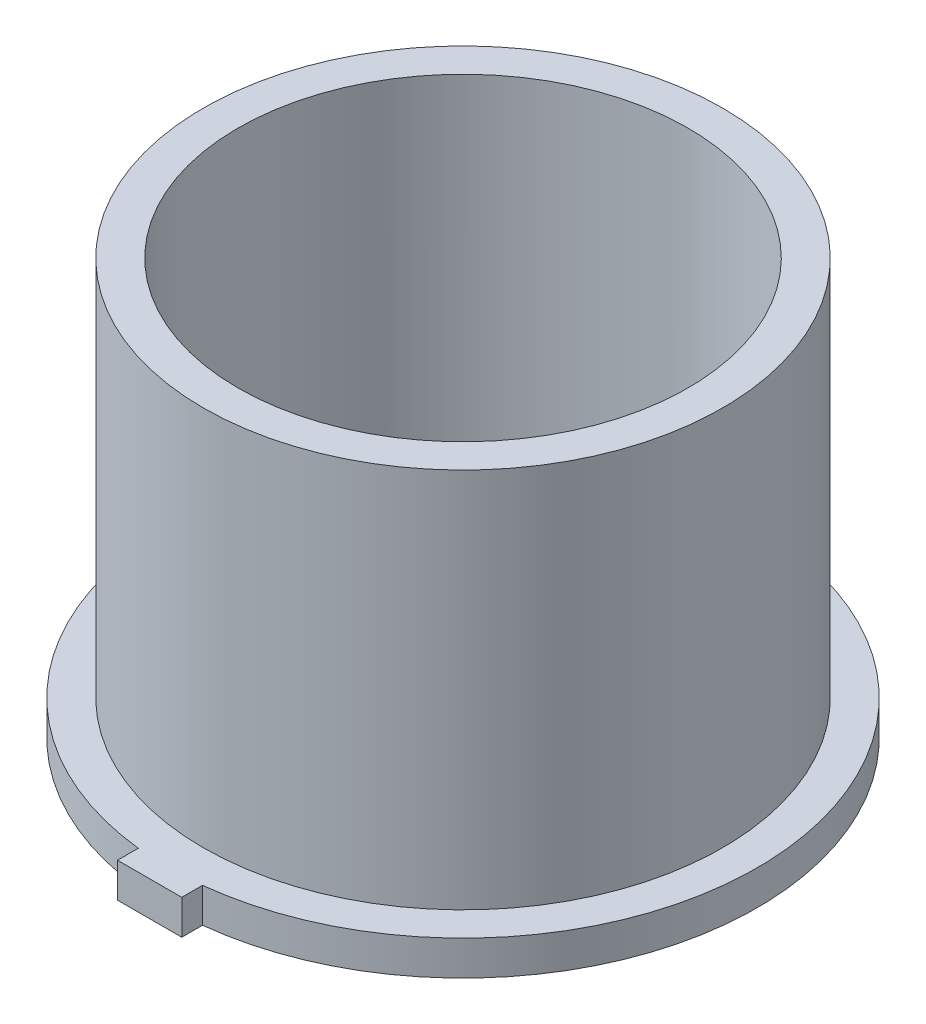
SolidWorks part; units mm, degrees
other "Markup1"
sketch "Sketch5" plane through (-30, 25, 30) normal (-0.0255, 0.5913, 0.806) x (0.9947, 0.0957, -0.0387)
ref_plane "Front Plane" through (0, 0, 0) normal (0, 0, 1) x (1, 0, 0)
ref_plane "Top Plane" through (0, 0, 0) normal (0, 1, 0) x (1, 0, 0)
ref_plane "Right Plane" through (0, 0, 0) normal (1, 0, 0) x (0, 0, -1)
sketch "Sketch1" plane through (0, 0, 0) normal (0, 1, 0) x (1, 0, 0)
  circle A0 centre (0, 0) radius 37.5
  circle A1 centre (0, 0) radius 32.5
  dimension "D1" = 65
  dimension "D2" = 75
sketch "Sketch4" plane through (0, 0, 0) normal (0, 1, 0) x (1, 0, 0)
  line L0 (0, 32.5) -> (0, -32.5) construction
  line L1 (-4.6363, 32.1676) -> (-4.6363, 9)
  line L2 (4.6363, 32.1676) -> (4.6363, 9)
  line L3 (4.6363, -9) -> (4.6363, -32.1676)
  line L4 (-10.3923, 0) -> (-5.1962, -9)
  line L5 (-5.1962, -9) -> (-4.6363, -9)
  line L6 (5.1962, -9) -> (10.3923, 0)
  line L7 (10.3923, 0) -> (5.1962, 9)
  line L8 (5.1962, 9) -> (4.6363, 9)
  line L9 (-5.1962, 9) -> (-10.3923, 0)
  line L10 (-4.6363, -9) -> (-4.6363, -32.1676)
  line L11 (4.6363, -9) -> (5.1962, -9)
  line L12 (-4.6363, 9) -> (-5.1962, 9)
  line L13 (-4.6363, -42.2464) -> (-4.6363, -45.2464)
  line L14 (-4.6363, -45.2464) -> (4.6363, -45.2464)
  line L15 (4.6363, -45.2464) -> (4.6363, -42.2464)
  line L16 (-10.3923, 0) -> (10.3923, 0) construction
  line L17 (-4.6363, 42.2464) -> (-4.6363, 45.2464)
  line L18 (-4.6363, 45.2464) -> (4.6363, 45.2464)
  line L19 (4.6363, 45.2464) -> (4.6363, 42.2464)
  arc A0 (4.6363, -42.2464) -> (4.6363, 42.2464) centre (0, 0) ccw
  arc A1 (4.6363, -32.1676) -> (4.6363, 32.1676) centre (0, 0) ccw
  arc A2 (-4.6363, 32.1676) -> (-4.6363, -32.1676) centre (0, 0) ccw
  circle A3 centre (0, 0) radius 9 construction
  arc A4 (-4.6363, 42.2464) -> (-4.6363, -42.2464) centre (0, 0) ccw
  dimension "D1" = 65
  dimension "D2" = 85
  dimension "D3" = 18
  dimension "D4" = 3
extrude "Boss-Extrude3" add sketch "Sketch4" along normal blind 5
ref_plane "Plane3" through (0, 0, 0) normal (0, -1, 0) x (-1, 0, 0)
sketch "Sketch7" plane through (0, 0, 0) normal (0, -1, 0) x (-1, 0, 0)
  line L1 (-7.5056, 0) -> (-3.7528, -6.5)
  line L2 (-3.7528, -6.5) -> (3.7528, -6.5)
  line L3 (3.7528, -6.5) -> (7.5056, 0)
  line L4 (7.5056, 0) -> (3.7528, 6.5)
  line L5 (3.7528, 6.5) -> (-3.7528, 6.5)
  line L6 (-3.7528, 6.5) -> (-7.5056, 0)
  circle A0 centre (0, 0) radius 6.5 construction
  dimension "D1" = 13
extrude "Cut-Extrude1" cut sketch "Sketch7" against normal through all
extrude "Boss-Extrude4" add sketch "Sketch1" along normal blind 60
equation "\"BallBearingDiameter\" = 22mm"
equation "\"SmallTubeOD\" = 75mm"
equation "\"SmallTubeID\"= \"SmallTubeOD\" - \"WallThickness\" * 2"
equation "\"D1@Sketch1\"=\"SmallTubeID\""
equation "\"D2@Sketch1\"=\"SmallTubeOD\""
equation "\"ZTravel\"= 20mm"
equation "\"WallThickness\"= 5mm"
equation "\"D1@Sketch4\"=\"SmallTubeID\""
equation "\"RestrictingFlangeOD\"= \"SmallTubeOD\" + 10mm"
equation "\"D2@Sketch4\"=\"RestrictingFlangeOD\""
equation "\"D1@Boss-Extrude3\"=\"WallThickness\""
equation "\"HexNutDiameter\" = 13mm"
equation "\"D1@Sketch7\"=\"HexNutDiameter\""
equation "\"D3@Sketch4\"=\"HexNutDiameter\"+5"
